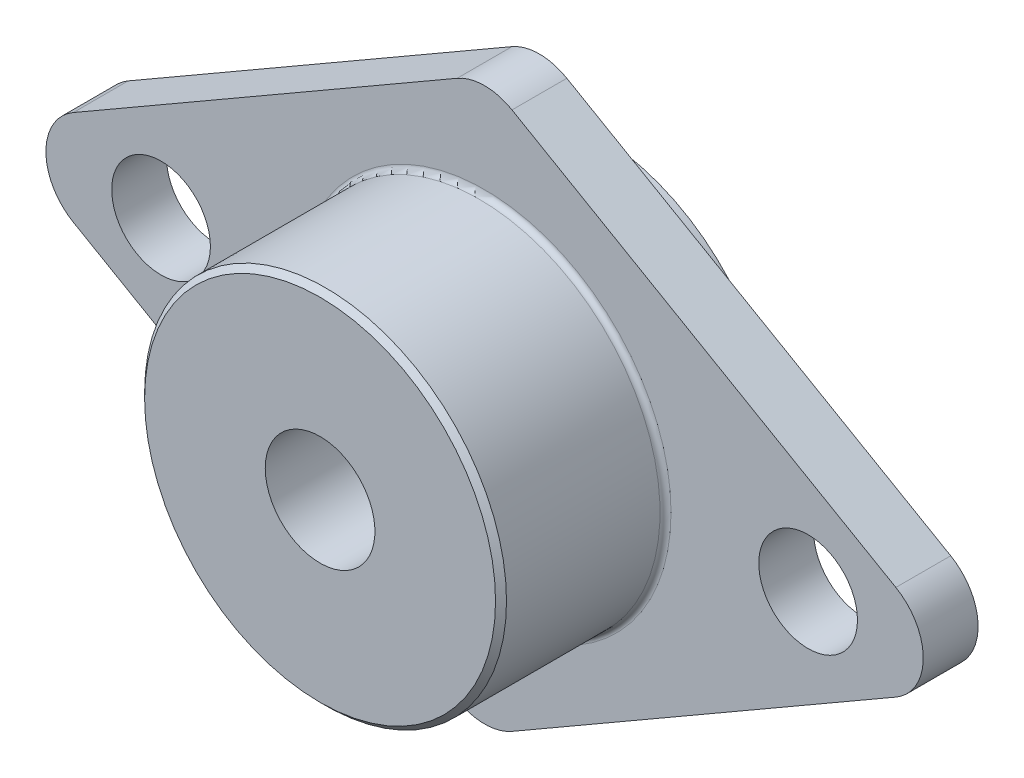
SolidWorks part; units mm, degrees
ref_plane "Plan de face" through (0, 0, 0) normal (0, 0, 1) x (1, 0, 0)
ref_plane "Plan de dessus" through (0, 0, 0) normal (0, 1, 0) x (1, 0, 0)
ref_plane "Plan de droite" through (0, 0, 0) normal (1, 0, 0) x (0, 0, -1)
sketch "Esquisse2" plane through (0, 0, 0) normal (0, 0, 1) x (1, 0, 0)
  line L0 (-37.5, 4.3301) -> (-2.5, 24.5374)
  line L1 (55, 0) -> (-55, 0) construction
  line L2 (0, -55) -> (0, 55) construction
  line L3 (2.5, 24.5374) -> (37.5, 4.3301)
  line L4 (37.5, -4.3301) -> (2.5, -24.5374)
  line L5 (-2.5, -24.5374) -> (-37.5, -4.3301)
  arc A0 (2.5, -24.5374) -> (-2.5, -24.5374) centre (0, -20.2073) cw
  arc A1 (2.5, 24.5374) -> (-2.5, 24.5374) centre (0, 20.2073) ccw
  arc A2 (37.5, 4.3301) -> (37.5, -4.3301) centre (35, 0) cw
  arc A3 (-37.5, 4.3301) -> (-37.5, -4.3301) centre (-35, 0) ccw
  point P10 (0, -25.9808)
  point P13 (0, 25.9808)
  point P16 (45, 0)
  point P19 (-45, 0)
  dimension "D4" = 5
  dimension "D1" = 60
  dimension "D2" = 60
  dimension "D3" = 45
extrude "Boss.-Extru.1" add sketch "Esquisse2" along normal blind 5
sketch "Esquisse3" plane through (0, 0, 5) normal (0, 0, 1) x (1, 0, 0)
  circle A0 centre (0, 0) radius 16.5
  dimension "D1" = 33
extrude "Boss.-Extru.2" add sketch "Esquisse3" along normal blind 15
sketch "Esquisse4" plane through (0, 0, 0) normal (0, 0, -1) x (-1, 0, 0)
  circle A0 centre (0, 0) radius 16.5
  dimension "D1" = 33
extrude "Boss.-Extru.3" add sketch "Esquisse4" along normal blind 5
sketch "Esquisse5" plane through (0, 0, -5) normal (0, 0, -1) x (-1, 0, 0)
  circle A0 centre (0, 0) radius 5
  dimension "D1" = 10
extrude "Enlèv. mat.-Extru.1" cut sketch "Esquisse5" against normal through all
sketch "Esquisse6" plane through (0, 0, 5) normal (0, 0, 1) x (1, 0, 0)
  circle A0 centre (29.5, 0) radius 4.5
  circle A1 centre (-29.5, 0) radius 4.5
  point P4 (0, 0)
  dimension "D1" = 59
  dimension "D2" = 9
  dimension "D3" = 9
  dimension "D4" = 29.5
extrude "Enlèv. mat.-Extru.2" cut sketch "Esquisse6" against normal blind 5
fillet "Congé1" radius 0.5 2 edges at (-16.5, 0, 0) (-16.5, 0, 5)
chamfer "Chanfrein1" distance 0.5 angle 45 1 edges at (16.5, 0, 20)
